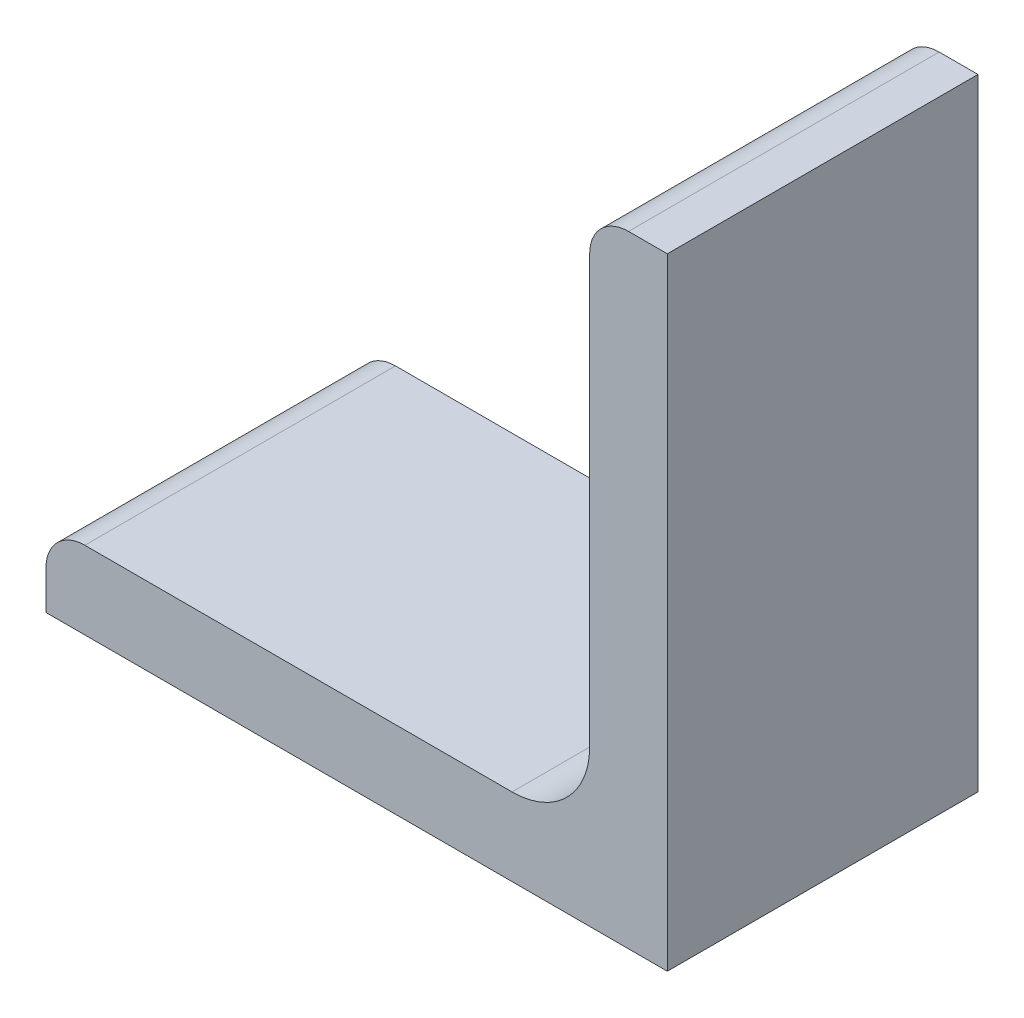
SolidWorks part; units mm, degrees
material "6061-T6 (SS)"
ref_plane "Front Plane" through (0, 0, 0) normal (0, 0, 1) x (1, 0, 0)
ref_plane "Top Plane" through (0, 0, 0) normal (0, 1, 0) x (1, 0, 0)
ref_plane "Right Plane" through (0, 0, 0) normal (1, 0, 0) x (0, 0, -1)
sketch "Sketch0" plane through (0, 0, 0) normal (0, 0, 1) x (1, 0, 0)
  line L0 (-12.7, -12.7) -> (12.7, -12.7)
  line L1 (12.7, -12.7) -> (12.7, 12.7)
  line L2 (12.7, 0) -> (0, 0) construction
  line L3 (0, 0) -> (0, -12.7) construction
  line L4 (9.525, -6.35) -> (9.525, 12.7) construction
  line L5 (6.35, -9.525) -> (-12.7, -9.525) construction
  arc A0 (9.525, -6.35) -> (6.35, -9.525) centre (6.35, -6.35) cw
  point P3 (8.5951, -8.5951)
  dimension "Inside Corner Radius" = 3.175
  dimension "Outside Height" = 25.4
  dimension "Inside Height" = 22.225
  dimension "Inside Width" = 22.225
  dimension "Wall Thickness" = 3.175
  dimension "D1" = 3.175
  dimension "Outside Width" = 25.4
sketch "Sketch1" plane through (0, 0, 0) normal (1, 0, 0) x (0, 0, -1)
  line L0 (152.4, 0) -> (-152.4, 0)
  point P4 (0, 0)
  dimension "Length" = 304.8
sketch "Sketch2" plane through (0, 0, 0) normal (0, 0, 1) x (1, 0, 0)
  line L0 (-12.7, -12.7) -> (12.7, -12.7)
  line L1 (12.7, -12.7) -> (12.7, 12.7)
  line L2 (12.7, 12.7) -> (9.525, 12.7) construction
  line L3 (9.525, 11.1125) -> (9.525, -6.35)
  line L4 (6.35, -9.525) -> (-11.1125, -9.525)
  line L5 (-12.7, -12.7) -> (-12.7, -9.525) construction
  line L6 (11.1125, 12.7) -> (12.7, 12.7)
  line L7 (-12.7, -11.1125) -> (-12.7, -12.7)
  line L8 (12.7, 0) -> (0, 0) construction
  line L9 (0, 0) -> (0, -12.7) construction
  arc A0 (9.525, 11.1125) -> (11.1125, 12.7) centre (11.1125, 11.1125) cw
  arc A1 (-12.7, -11.1125) -> (-11.1125, -9.525) centre (-11.1125, -11.1125) cw
  arc A2 (9.525, -6.35) -> (6.35, -9.525) centre (6.35, -6.35) cw
  dimension "Inside Radius" = 3.175
  dimension "Height" = 25.4
  dimension "Width" = 25.4
  dimension "Thickness" = 3.175
extrude "Boss-Extrude1" add sketch "Sketch2" along normal mid plane 304.8
sketch "Break Locations" plane through (0, 0, 0) normal (1, 0, 0) x (0, 0, -1)
  line L0 (-126.492, 0) -> (126.492, 0)
  line L1 (-152.4, -12.7) -> (-152.4, 12.7) construction
  line L2 (152.4, -12.7) -> (152.4, 12.7) construction
  point P0 (-130.81, 0)
  point P1 (130.81, 0)
  point P10 (0, 0)
  point P11 (126.492, 0)
  point P13 (-126.492, 0)
  dimension "D1" = 21.59
  dimension "D2" = 21.59
  dimension "D3" = 25.908
sketch "Sketch3" plane through (0, -12.7, 0) normal (0, -1, 0) x (1, 0, 0)
  line L0 (6.35, 152.4) -> (-11.1125, 152.4) construction
  line L1 (-18.6199, -154.8304) -> (17.512, -154.8304)
  line L2 (-18.6199, -154.8304) -> (-18.6199, 139.7)
  line L3 (-18.6199, 139.7) -> (17.512, 139.7)
  line L4 (17.512, -154.8304) -> (17.512, 139.7)
  dimension "D1" = 12.7
extrude "Cut-Extrude1" cut sketch "Sketch3" against normal through all
equation "\"D1@Break Locations\" = .85 * \"Height@Sketch2\""
equation "\"D2@Break Locations\"=\"D1@Break Locations\""
equation "\"Thickness@Sketch2\"=\"wall thickness@sketch0\""
equation "\"Height@Sketch2\"=\"outside height@sketch0\""
equation "\"Width@Sketch2\"=\"outside width@sketch0\""
equation "\"Inside Radius@Sketch2\"=\"inside corner radius@sketch0\""
equation "\"Length@Boss-Extrude1\"=\"length@sketch1\""
equation "\"D3@Break Locations\"=\"D2@Break Locations\"*1.2"
equation "\"D1@Sketch0\"=\"Wall Thickness@Sketch0\""
